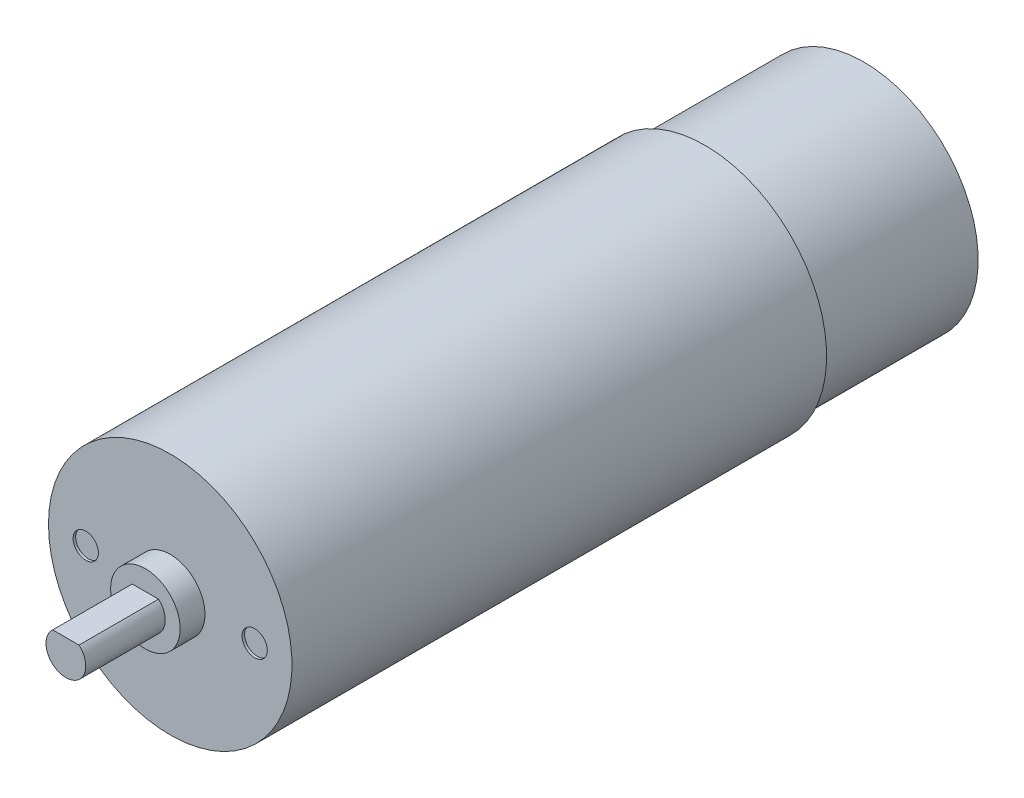
SolidWorks part; units mm, degrees
material "Custom Plastic"
ref_plane "Front Plane" through (0, 0, 0) normal (0, 0, 1) x (1, 0, 0)
ref_plane "Top Plane" through (0, 0, 0) normal (0, 1, 0) x (1, 0, 0)
ref_plane "Right Plane" through (0, 0, 0) normal (1, 0, 0) x (0, 0, -1)
sketch "Sketch1" plane through (0, 0, 0) normal (0, 0, 1) x (1, 0, 0)
  circle A0 centre (0, 0) radius 2
  dimension "D1" = 4
extrude "Boss-Extrude1" add sketch "Sketch1" along normal blind 8
sketch "Sketch2" plane through (0, 0, 0) normal (0, 0, -1) x (-1, 0, 0)
  circle A0 centre (0, 0) radius 3.5
  dimension "D1" = 7
extrude "Boss-Extrude2" add sketch "Sketch2" along normal blind 2.5
sketch "Sketch3" plane through (0, 0, -2.5) normal (0, 0, -1) x (-1, 0, 0)
  circle A0 centre (0, 0) radius 12.25
  dimension "D1" = 24.5
extrude "Boss-Extrude3" add sketch "Sketch3" along normal blind 53.8
sketch "Sketch4" plane through (0, 0, -2.5) normal (0, 0, 1) x (1, 0, 0)
  circle A0 centre (8.5, 0) radius 1.27
  circle A1 centre (-8.5, 0) radius 1.27
  dimension "D1" = 2.54
  dimension "D2" = 2.54
  dimension "D3" = 17
  dimension "D4" = 8.5
extrude "Cut-Extrude1" cut sketch "Sketch4" against normal blind 0.254
sketch "Sketch5" plane through (0, 0, -56.3) normal (0, 0, -1) x (-1, 0, 0)
  circle A0 centre (0, 0) radius 11.5
  dimension "D1" = 23
extrude "Boss-Extrude4" add sketch "Sketch5" along normal blind 16
sketch "Sketch6" plane through (0, 0, 8) normal (0, 0, 1) x (1, 0, 0)
  line L0 (-1.3229, 1.5) -> (1.3229, 1.5)
  circle A0 centre (0, 0) radius 2 construction
  arc A1 (-1.3229, 1.5) -> (1.3229, 1.5) centre (0, 0) cw
  dimension "D1" = 1.5
extrude "Cut-Extrude2" cut sketch "Sketch6" against normal blind 8
